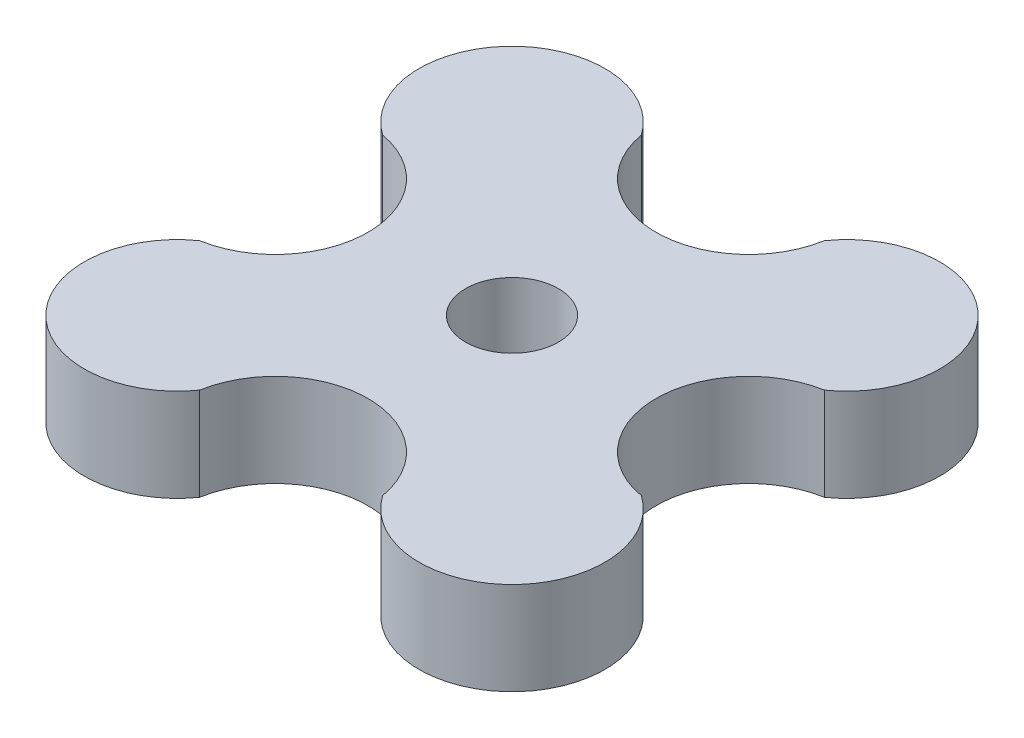
SolidWorks part; units mm, degrees
material "1060 Alloy"
ref_plane "Front" through (0, 0, 0) normal (0, 0, 1) x (1, 0, 0)
ref_plane "Top" through (0, 0, 0) normal (0, 1, 0) x (1, 0, 0)
ref_plane "Right" through (0, 0, 0) normal (1, 0, 0) x (0, 0, -1)
sketch "Sketch1" plane through (0, 0, 0) normal (0, 1, 0) x (1, 0, 0)
  line L0 (0, -55) -> (0, 55) construction
  line L1 (-55, 0) -> (55, 0) construction
  circle A0 centre (0, 0) radius 12.75
  circle A1 centre (0, 12.75) radius 5
  circle A2 centre (9.0156, 9.0156) radius 5
  circle A3 centre (12.75, 0) radius 5
  circle A4 centre (9.0156, -9.0156) radius 5
  circle A5 centre (0, -12.75) radius 5
  circle A6 centre (-9.0156, -9.0156) radius 5
  circle A7 centre (-12.75, 0) radius 5
  circle A8 centre (-9.0156, 9.0156) radius 5
  point P22 (-0.1698, -0.1142)
  point P23 (0, 0)
  dimension "D1" = 25.5
  dimension "D2" = 10
  dimension "D4" = 9.0156
  dimension "D5" = 9.0156
  dimension "D3" = 8
extrude "Boss-Extrude1" add sketch "Sketch1" along normal blind 5 contours A8 A7 A6 A5 A4 A3 A2 A1 | A7 A8 A1 A0 | A1 A8 A7 A0 | A3 A0 A1 A2 | A3 A2 A1 A0 | A5 A0 A3 A4 | A5 A4 A3 A0 | A7 A0 A5 A6 | A7 A6 A5 A0
sketch "Sketch2" plane through (0, 5, 0) normal (0, 1, 0) x (1, 0, 0)
  circle A0 centre (0, 0) radius 2.5
  dimension "D1" = 5
extrude "Cut-Extrude1" cut sketch "Sketch2" against normal blind 5 contours A0
